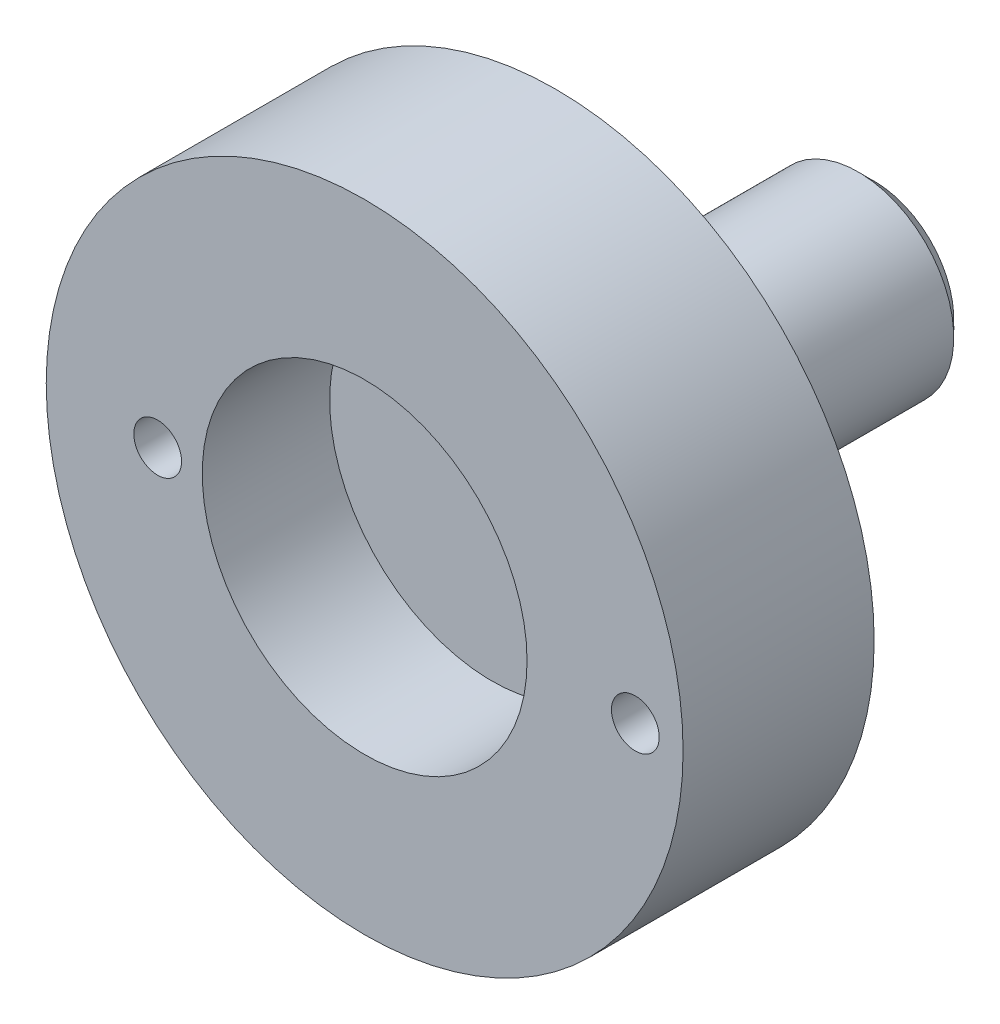
SolidWorks part; units mm, degrees
ref_plane "Front Plane" through (0, 0, 0) normal (0, 0, 1) x (1, 0, 0)
ref_plane "Top Plane" through (0, 0, 0) normal (0, 1, 0) x (1, 0, 0)
ref_plane "Right Plane" through (0, 0, 0) normal (1, 0, 0) x (0, 0, -1)
sketch "Sketch1" plane through (0, 0, 0) normal (0, 0, 1) x (1, 0, 0)
  circle A0 centre (0, 0) radius 5.1
  circle A1 centre (0, 0) radius 10
  dimension "D1" = 10.2
  dimension "D2" = 20
extrude "Boss-Extrude1" add sketch "Sketch1" along normal blind 4
sketch "Sketch3" plane through (0, 0, 0) normal (0, 0, -1) x (-1, 0, 0)
  circle A0 centre (0, 0) radius 3
  dimension "D1" = 6
extrude "Boss-Extrude2" add sketch "Sketch3" along normal blind 12 separate body
sketch "Sketch4" plane through (0, 0, 0) normal (0, 0, -1) x (-1, 0, 0)
  circle A0 centre (0, 0) radius 10 construction
  circle A2 centre (0, 0) radius 10
  circle A4 centre (0, 0) radius 3 construction
  circle A5 centre (0, 0) radius 3
extrude "Boss-Extrude3" add sketch "Sketch4" along normal blind 2
chamfer "Chamfer2" distance 1 angle 45 1 edges at (-3, 0, -2)
chamfer "Chamfer4" distance 0.5 angle 45 1 edges at (-3, 0, -12)
sketch "Sketch5" plane through (0, 0, -2) normal (0, 0, -1) x (-1, 0, 0)
  line L0 (-10, 0) -> (10, 0) construction
  circle A0 centre (0, 0) radius 10 construction
  circle A1 centre (-8.5, 0) radius 0.75
  circle A2 centre (6.5, 0) radius 0.75
  circle A3 centre (0, 0) radius 4 construction
  point P9 (4, 0)
  dimension "D1" = 1.5
  dimension "D2" = 1.5
  dimension "D3" = 1.5
  dimension "D4" = 2.5
extrude "Cut-Extrude1" cut sketch "Sketch5" against normal up to next
